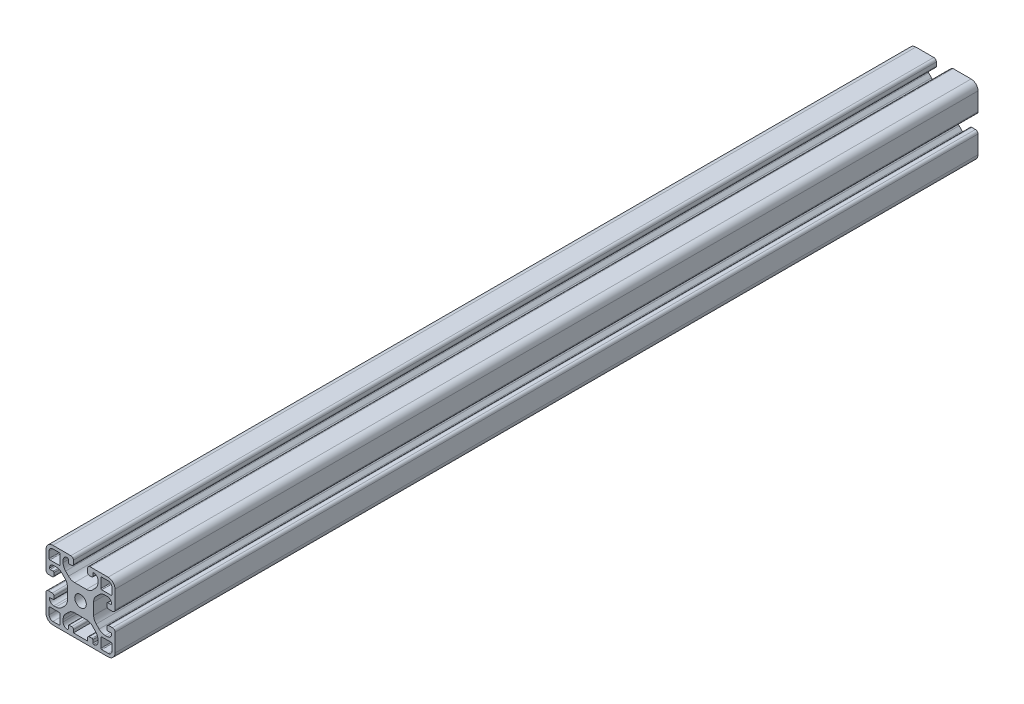
SolidWorks part; units mm, degrees
ref_plane "Ebene vorne" through (0, 0, 0) normal (0, 0, 1) x (1, 0, 0)
ref_plane "Ebene oben" through (0, 0, 0) normal (0, 1, 0) x (1, 0, 0)
ref_plane "Ebene rechts" through (0, 0, 0) normal (1, 0, 0) x (0, 0, -1)
ref_plane "Ebene1" through (0, 0, 1000) normal (0, 0, 1) x (1, 0, 0)
sketch "Skizze1" plane through (0, 0, 1000) normal (0, 0, 1) x (1, 0, 0)
  line L0 (27.8, 32.3) -> (27.8, 37.7)
  line L1 (28.3, 38.2) -> (32, 38.2)
  line L2 (34.2, 36) -> (34.2, 32.3)
  line L3 (33.7, 31.8) -> (28.3, 31.8)
  line L4 (28.3, 8.2) -> (33.7, 8.2)
  line L5 (34.2, 7.7) -> (34.2, 4)
  line L6 (32, 1.8) -> (28.3, 1.8)
  line L7 (27.8, 2.3) -> (27.8, 7.7)
  line L8 (3.7, 31.8) -> (-1.7, 31.8)
  line L9 (-2.2, 32.3) -> (-2.2, 36)
  line L10 (0, 38.2) -> (3.7, 38.2)
  line L11 (4.2, 37.7) -> (4.2, 32.3)
  line L12 (4.2, 7.7) -> (4.2, 2.3)
  line L13 (3.7, 1.8) -> (0, 1.8)
  line L14 (-2.2, 4) -> (-2.2, 7.7)
  line L15 (-1.7, 8.2) -> (3.7, 8.2)
  line L16 (20.1, 2) -> (11.9, 2)
  line L17 (11.9, 2) -> (11.9, 3.65)
  line L18 (10.9, 4.65) -> (9.4, 4.65)
  line L19 (8.9, 4.15) -> (8.9, 2.5)
  line L20 (5.9, 4.5) -> (5.9, 5.7076)
  line L21 (7.3645, 9.2431) -> (9.0569, 10.9355)
  line L22 (12.5924, 12.4) -> (19.4076, 12.4)
  line L23 (22.9431, 10.9355) -> (24.6355, 9.2431)
  line L24 (26.1, 5.7076) -> (26.1, 4.5)
  line L25 (23.1, 2.5) -> (23.1, 4.15)
  line L26 (22.6, 4.65) -> (21.1, 4.65)
  line L27 (20.1, 3.65) -> (20.1, 2)
  line L28 (5.9, 34.2924) -> (5.9, 35.5)
  line L29 (8.9, 37.5) -> (8.9, 35.85)
  line L30 (9.4, 35.35) -> (10.9, 35.35)
  line L31 (11.9, 36.35) -> (11.9, 38.5)
  line L32 (10.4, 40) -> (0, 40)
  line L33 (-4, 36) -> (-4, 25.6)
  line L34 (-2.5, 24.1) -> (-0.35, 24.1)
  line L35 (0.65, 25.1) -> (0.65, 26.6)
  line L36 (0.15, 27.1) -> (-1.5, 27.1)
  line L37 (0.5, 30.1) -> (1.7076, 30.1)
  line L38 (5.2431, 28.6355) -> (6.9355, 26.9431)
  line L39 (8.4, 23.4076) -> (8.4, 16.5924)
  line L40 (6.9355, 13.0569) -> (5.2431, 11.3645)
  line L41 (1.7076, 9.9) -> (0.5, 9.9)
  line L42 (-1.5, 12.9) -> (0.15, 12.9)
  line L43 (0.65, 13.4) -> (0.65, 14.9)
  line L44 (-0.35, 15.9) -> (-2.5, 15.9)
  line L45 (-4, 14.4) -> (-4, 4)
  line L46 (0, 0) -> (32, 0)
  line L47 (36, 4) -> (36, 14.4)
  line L48 (34.5, 15.9) -> (32.35, 15.9)
  line L49 (31.35, 14.9) -> (31.35, 13.4)
  line L50 (31.85, 12.9) -> (33.5, 12.9)
  line L51 (31.5, 9.9) -> (30.2924, 9.9)
  line L52 (26.7569, 11.3645) -> (25.0645, 13.0569)
  line L53 (23.6, 16.5924) -> (23.6, 23.4076)
  line L54 (25.0645, 26.9431) -> (26.7569, 28.6355)
  line L55 (30.2924, 30.1) -> (31.5, 30.1)
  line L56 (33.5, 27.1) -> (31.85, 27.1)
  line L57 (31.35, 26.6) -> (31.35, 25.1)
  line L58 (32.35, 24.1) -> (34.5, 24.1)
  line L59 (36, 25.6) -> (36, 36)
  line L60 (32, 40) -> (21.6, 40)
  line L61 (20.1, 38.5) -> (20.1, 36.35)
  line L62 (21.1, 35.35) -> (22.6, 35.35)
  line L63 (23.1, 35.85) -> (23.1, 37.5)
  line L64 (26.1, 35.5) -> (26.1, 34.2924)
  line L65 (24.6355, 30.7569) -> (22.9431, 29.0645)
  line L66 (19.4076, 27.6) -> (12.5924, 27.6)
  line L67 (9.0569, 29.0645) -> (7.3645, 30.7569)
  circle A0 centre (16, 20) radius 3.35
  arc A1 (28.3, 31.8) -> (27.8, 32.3) centre (28.3, 32.3) cw
  arc A2 (27.8, 37.7) -> (28.3, 38.2) centre (28.3, 37.7) cw
  arc A3 (32, 38.2) -> (34.2, 36) centre (32, 36) cw
  arc A4 (34.2, 32.3) -> (33.7, 31.8) centre (33.7, 32.3) cw
  arc A5 (27.8, 7.7) -> (28.3, 8.2) centre (28.3, 7.7) cw
  arc A6 (33.7, 8.2) -> (34.2, 7.7) centre (33.7, 7.7) cw
  arc A7 (34.2, 4) -> (32, 1.8) centre (32, 4) cw
  arc A8 (28.3, 1.8) -> (27.8, 2.3) centre (28.3, 2.3) cw
  arc A9 (4.2, 32.3) -> (3.7, 31.8) centre (3.7, 32.3) cw
  arc A10 (-1.7, 31.8) -> (-2.2, 32.3) centre (-1.7, 32.3) cw
  arc A11 (-2.2, 36) -> (0, 38.2) centre (0, 36) cw
  arc A12 (3.7, 38.2) -> (4.2, 37.7) centre (3.7, 37.7) cw
  arc A13 (3.7, 8.2) -> (4.2, 7.7) centre (3.7, 7.7) cw
  arc A14 (4.2, 2.3) -> (3.7, 1.8) centre (3.7, 2.3) cw
  arc A15 (0, 1.8) -> (-2.2, 4) centre (0, 4) cw
  arc A16 (-2.2, 7.7) -> (-1.7, 8.2) centre (-1.7, 7.7) cw
  arc A17 (11.9, 3.65) -> (10.9, 4.65) centre (10.9, 3.65) ccw
  arc A18 (9.4, 4.65) -> (8.9, 4.15) centre (9.4, 4.15) ccw
  arc A19 (8.9, 2.5) -> (8.4, 2) centre (8.4, 2.5) cw
  arc A20 (8.4, 2) -> (5.9, 4.5) centre (8.4, 4.5) cw
  arc A21 (5.9, 5.7076) -> (7.3645, 9.2431) centre (10.9, 5.7076) cw
  arc A22 (9.0569, 10.9355) -> (12.5924, 12.4) centre (12.5924, 7.4) cw
  arc A23 (19.4076, 12.4) -> (22.9431, 10.9355) centre (19.4076, 7.4) cw
  arc A24 (24.6355, 9.2431) -> (26.1, 5.7076) centre (21.1, 5.7076) cw
  arc A25 (26.1, 4.5) -> (23.6, 2) centre (23.6, 4.5) cw
  arc A26 (23.6, 2) -> (23.1, 2.5) centre (23.6, 2.5) cw
  arc A27 (23.1, 4.15) -> (22.6, 4.65) centre (22.6, 4.15) ccw
  arc A28 (21.1, 4.65) -> (20.1, 3.65) centre (21.1, 3.65) ccw
  arc A29 (7.3645, 30.7569) -> (5.9, 34.2924) centre (10.9, 34.2924) cw
  arc A30 (5.9, 35.5) -> (8.4, 38) centre (8.4, 35.5) cw
  arc A31 (8.4, 38) -> (8.9, 37.5) centre (8.4, 37.5) cw
  arc A32 (8.9, 35.85) -> (9.4, 35.35) centre (9.4, 35.85) ccw
  arc A33 (10.9, 35.35) -> (11.9, 36.35) centre (10.9, 36.35) ccw
  arc A34 (11.9, 38.5) -> (10.4, 40) centre (10.4, 38.5) ccw
  arc A35 (0, 40) -> (-4, 36) centre (0, 36) ccw
  arc A36 (-4, 25.6) -> (-2.5, 24.1) centre (-2.5, 25.6) ccw
  arc A37 (-0.35, 24.1) -> (0.65, 25.1) centre (-0.35, 25.1) ccw
  arc A38 (0.65, 26.6) -> (0.15, 27.1) centre (0.15, 26.6) ccw
  arc A39 (-1.5, 27.1) -> (-2, 27.6) centre (-1.5, 27.6) cw
  arc A40 (-2, 27.6) -> (0.5, 30.1) centre (0.5, 27.6) cw
  arc A41 (1.7076, 30.1) -> (5.2431, 28.6355) centre (1.7076, 25.1) cw
  arc A42 (6.9355, 26.9431) -> (8.4, 23.4076) centre (3.4, 23.4076) cw
  arc A43 (8.4, 16.5924) -> (6.9355, 13.0569) centre (3.4, 16.5924) cw
  arc A44 (5.2431, 11.3645) -> (1.7076, 9.9) centre (1.7076, 14.9) cw
  arc A45 (0.5, 9.9) -> (-2, 12.4) centre (0.5, 12.4) cw
  arc A46 (-2, 12.4) -> (-1.5, 12.9) centre (-1.5, 12.4) cw
  arc A47 (0.15, 12.9) -> (0.65, 13.4) centre (0.15, 13.4) ccw
  arc A48 (0.65, 14.9) -> (-0.35, 15.9) centre (-0.35, 14.9) ccw
  arc A49 (-2.5, 15.9) -> (-4, 14.4) centre (-2.5, 14.4) ccw
  arc A50 (-4, 4) -> (0, 0) centre (0, 4) ccw
  arc A51 (32, 0) -> (36, 4) centre (32, 4) ccw
  arc A52 (36, 14.4) -> (34.5, 15.9) centre (34.5, 14.4) ccw
  arc A53 (32.35, 15.9) -> (31.35, 14.9) centre (32.35, 14.9) ccw
  arc A54 (31.35, 13.4) -> (31.85, 12.9) centre (31.85, 13.4) ccw
  arc A55 (33.5, 12.9) -> (34, 12.4) centre (33.5, 12.4) cw
  arc A56 (34, 12.4) -> (31.5, 9.9) centre (31.5, 12.4) cw
  arc A57 (30.2924, 9.9) -> (26.7569, 11.3645) centre (30.2924, 14.9) cw
  arc A58 (25.0645, 13.0569) -> (23.6, 16.5924) centre (28.6, 16.5924) cw
  arc A59 (23.6, 23.4076) -> (25.0645, 26.9431) centre (28.6, 23.4076) cw
  arc A60 (26.7569, 28.6355) -> (30.2924, 30.1) centre (30.2924, 25.1) cw
  arc A61 (31.5, 30.1) -> (34, 27.6) centre (31.5, 27.6) cw
  arc A62 (34, 27.6) -> (33.5, 27.1) centre (33.5, 27.6) cw
  arc A63 (31.85, 27.1) -> (31.35, 26.6) centre (31.85, 26.6) ccw
  arc A64 (31.35, 25.1) -> (32.35, 24.1) centre (32.35, 25.1) ccw
  arc A65 (34.5, 24.1) -> (36, 25.6) centre (34.5, 25.6) ccw
  arc A66 (36, 36) -> (32, 40) centre (32, 36) ccw
  arc A67 (21.6, 40) -> (20.1, 38.5) centre (21.6, 38.5) ccw
  arc A68 (20.1, 36.35) -> (21.1, 35.35) centre (21.1, 36.35) ccw
  arc A69 (22.6, 35.35) -> (23.1, 35.85) centre (22.6, 35.85) ccw
  arc A70 (23.1, 37.5) -> (23.6, 38) centre (23.6, 37.5) cw
  arc A71 (23.6, 38) -> (26.1, 35.5) centre (23.6, 35.5) cw
  arc A72 (26.1, 34.2924) -> (24.6355, 30.7569) centre (21.1, 34.2924) cw
  arc A73 (22.9431, 29.0645) -> (19.4076, 27.6) centre (19.4076, 32.6) cw
  arc A74 (12.5924, 27.6) -> (9.0569, 29.0645) centre (12.5924, 32.6) cw
extrude "Aufsatz-Linear austragen1" add sketch "Skizze1" against normal blind 500
